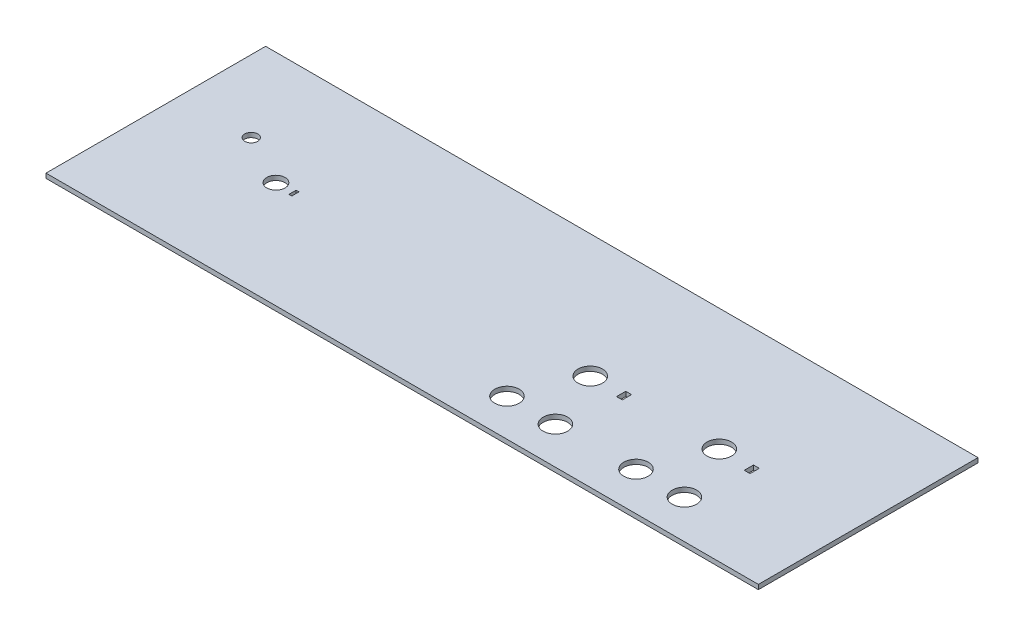
SolidWorks part; units mm, degrees
ref_plane "Front Plane" through (0, 0, 0) normal (0, 0, 1) x (1, 0, 0)
ref_plane "Top Plane" through (0, 0, 0) normal (0, 1, 0) x (1, 0, 0)
ref_plane "Right Plane" through (0, 0, 0) normal (1, 0, 0) x (0, 0, -1)
sketch "Sketch1" plane through (0, 0, 0) normal (0, 1, 0) x (1, 0, 0)
  line L1 (0, 0) -> (247.65, 0)
  line L2 (0, 0) -> (0, 76.3524)
  line L3 (0, 76.3524) -> (247.65, 76.3524)
  line L4 (247.65, 0) -> (247.65, 76.3524)
  line L11 (210.8551, 31.8967) -> (212.8551, 31.8967)
  line L12 (210.8551, 31.8967) -> (210.8551, 35.0967)
  line L13 (210.8551, 35.0967) -> (212.8551, 35.0967)
  line L14 (212.8551, 31.8967) -> (212.8551, 35.0967)
  line L17 (166.4553, 31.8967) -> (168.4553, 31.8967)
  line L18 (166.4553, 31.8967) -> (166.4553, 35.0967)
  line L19 (166.4553, 35.0967) -> (168.4553, 35.0967)
  line L20 (168.4553, 31.8967) -> (168.4553, 35.0967)
  line L24 (48.6282, 35.8258) -> (49.6282, 35.8258)
  line L25 (48.6282, 35.8258) -> (48.6282, 38.3258)
  line L26 (48.6282, 38.3258) -> (49.6282, 38.3258)
  line L27 (49.6282, 35.8258) -> (49.6282, 38.3258)
  circle A0 centre (208.5188, 13.4166) radius 4.25
  circle A1 centre (191.6913, 13.4166) radius 4.25
  circle A2 centre (164.119, 12.9682) radius 4.25
  circle A3 centre (147.2915, 12.9682) radius 4.25
  circle A4 centre (200.1051, 33.9633) radius 4.25
  circle A5 centre (155.7053, 33.4967) radius 4.25
  circle A6 centre (25, 46.3524) radius 2.25
  circle A7 centre (42.8532, 37.0758) radius 3.175
  point P14 (0, 0)
  dimension "D3" = 8.5
  dimension "D4" = 8.5
  dimension "D5" = 8.5
  dimension "D6" = 8.5
  dimension "D7" = 16.8275
  dimension "D8" = 16.8275
  dimension "D9" = 8.5
  dimension "D10" = 8.5
  dimension "D11" = 10.75
  dimension "D18" = 4.5
  dimension "D19" = 6.35
  dimension "D1" = 76.3524
  dimension "D2" = 247.65
  dimension "D12" = 2
  dimension "D13" = 3.2
  dimension "D14" = 10.75
  dimension "D15" = 2
  dimension "D16" = 3.2
  dimension "D17" = 25
  dimension "D20" = 5.775
  dimension "D21" = 2.5
  dimension "D22" = 1
  dimension "D23" = 30
extrude "Boss-Extrude1" add sketch "Sketch1" along normal blind 1.6
